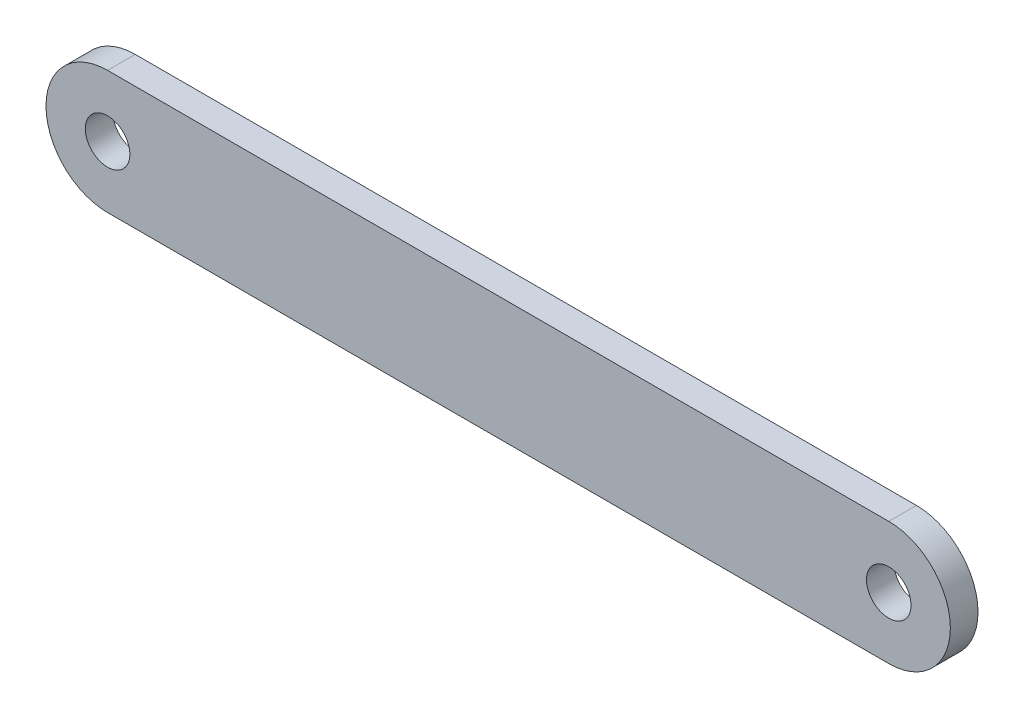
SolidWorks part; units mm, degrees
ref_plane "Alzado" through (0, 0, 0) normal (0, 0, 1) x (1, 0, 0)
ref_plane "Planta" through (0, 0, 0) normal (0, 1, 0) x (1, 0, 0)
ref_plane "Vista lateral" through (0, 0, 0) normal (1, 0, 0) x (0, 0, -1)
sketch "Croquis1" plane through (0, 0, 0) normal (0, 0, 1) x (1, 0, 0)
  line L0 (0, 0) -> (59.61, 0) construction
  line L1 (29.805, 0) -> (29.805, 7.2722) construction
  line L2 (0, 0) -> (59.61, 0) construction
  line L3 (0, 4.7) -> (59.61, 4.7)
  line L4 (0, -4.7) -> (59.61, -4.7)
  circle A0 centre (0, 0) radius 1.7
  circle A1 centre (59.61, 0) radius 1.7
  arc A2 (0, 4.7) -> (0, -4.7) centre (0, 0) ccw
  arc A3 (59.61, -4.7) -> (59.61, 4.7) centre (59.61, 0) ccw
  point P7 (29.805, 0)
  dimension "D2" = 3.4
  dimension "D3" = 3
  dimension "D1" = 59.61
extrude "Saliente-Extruir1" add sketch "Croquis1" along normal blind 2.11
